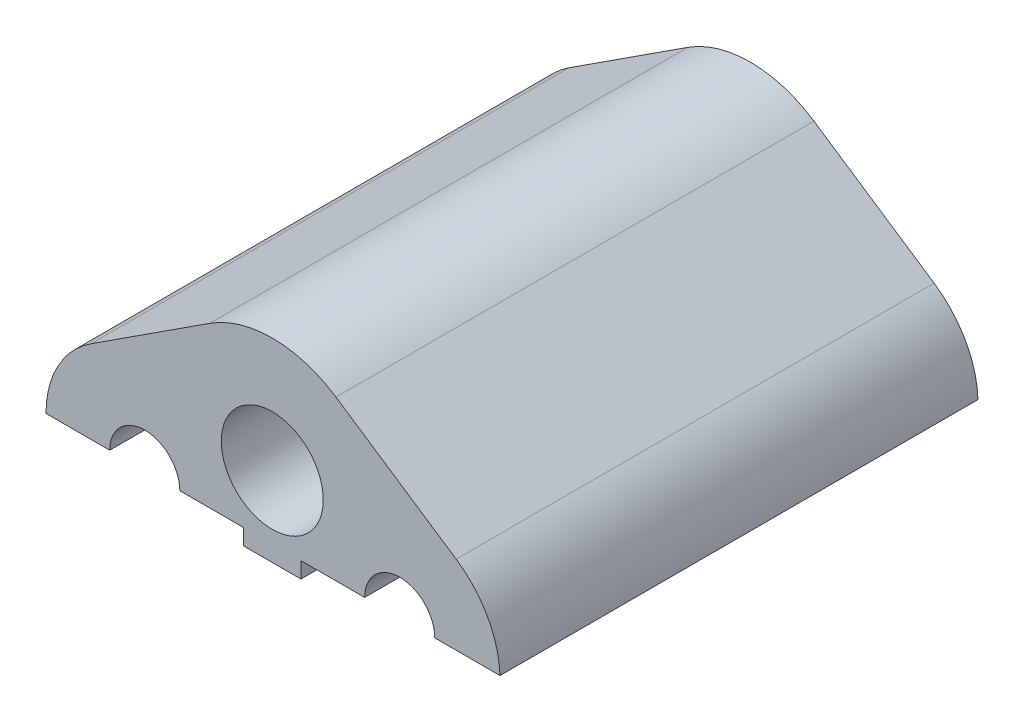
SolidWorks part; units mm, degrees
ref_plane "Front Plane" through (0, 0, 0) normal (0, 0, 1) x (1, 0, 0)
ref_plane "Top Plane" through (0, 0, 0) normal (0, 1, 0) x (1, 0, 0)
ref_plane "Right Plane" through (0, 0, 0) normal (1, 0, 0) x (0, 0, -1)
sketch "Sketch1" plane through (0, 0, 0) normal (0, 0, 1) x (1, 0, 0)
  line L0 (-1.6124, 5.0197) -> (-5.3402, 2.6003)
  line L1 (-3.6526, -3.1) -> (4.396, -3.2018)
  line L3 (2.3464, 4.994) -> (6.1173, 2.4763)
  circle A0 centre (-3.6526, 0) radius 1.1
  circle A1 centre (4.3474, 0) radius 1.1
  arc A2 (-3.0961, 3.0497) -> (-0.879, -1.3847) centre (-3.6526, 0) ccw
  circle A4 centre (0.3474, 2) radius 1.6
  arc A5 (-0.879, -1.3847) -> (1.5739, -1.3847) centre (0.3474, 2) ccw
  circle A6 centre (-3.6526, 0) radius 3.1 construction
  arc A9 (1.5739, -1.3847) -> (3.8214, 2.9444) centre (4.396, -0.1018) ccw
  circle A10 centre (0.3474, 2) radius 3.6 construction
  arc A12 (3.8214, 2.9444) -> (-3.0961, 3.0497) centre (0.3474, 2) ccw
  dimension "D1" = 2.2
  dimension "D2" = 2.2
  dimension "D5" = 3.2
  dimension "D3" = 8
  dimension "D6" = 2
  dimension "D4" = 2
  dimension "D7" = 2
extrude "Boss-Extrude1" add sketch "Sketch1" along normal blind 15 contours A9 A5 A2 L1 | A9 A12 A2 A5 L1 A0 A1 A4 | A12 A9 L3 | A12 L0 A2
sketch "Sketch3" plane through (0, 0, 15) normal (0, 0, 1) x (1, 0, 0)
  line L1 (-3.6526, 0) -> (12.6552, 0)
  line L2 (-3.6526, 0) -> (-3.6526, -4.7746)
  line L3 (-3.6526, -4.7746) -> (12.6552, -4.7746)
  line L4 (12.6552, 0) -> (12.6552, -4.7746)
  line L5 (-3.6526, 0) -> (-12.2596, 0)
  line L6 (-3.6526, 0) -> (-3.6526, -4.7746)
  line L7 (-3.6526, -4.7746) -> (-12.2596, -4.7746)
  line L8 (-12.2596, 0) -> (-12.2596, -4.7746)
  line M1 (-3.6526, -3.1) -> (4.396, -3.2018)
  arc M2 (4.396, -3.2018) -> (6.1173, 2.4763) centre (4.396, -0.1018) ccw
  arc M6 (-5.3402, 2.6003) -> (-3.6526, -3.1) centre (-3.6526, 0) ccw
  circle M7 centre (-3.6526, 0) radius 1.1
  circle M8 centre (4.3474, 0) radius 1.1
extrude "Cut-Extrude1" cut sketch "Sketch3" against normal blind 15 contours L5 L2 M7 M6 | L2 L1 M7 M1 M2 M8 | L5 L8 L7 L2 M6 | L4 L1 L2 L3 M2 M1
sketch "Sketch4" plane through (0, 0, 15) normal (0, 0, 1) x (1, 0, 0)
  line L0 (-2.5526, 0) -> (3.2474, 0) construction
  line L1 (-0.5526, -0.5) -> (1.2474, -0.5)
  line L2 (-0.5526, -0.5) -> (-0.5526, 0)
  line L3 (-0.5526, 0) -> (1.2474, 0)
  line L4 (1.2474, -0.5) -> (1.2474, 0)
  line L5 (-0.5526, -0.5) -> (1.2474, 0) construction
  line L6 (-0.5526, 0) -> (1.2474, -0.5) construction
  point P0 (0.3474, -0.25)
  dimension "D1" = 0.5
  dimension "D2" = 1.8
extrude "Boss-Extrude2" add sketch "Sketch4" against normal up to surface (15 mm away) up to face at (0.3616, 1.8229, 0)
